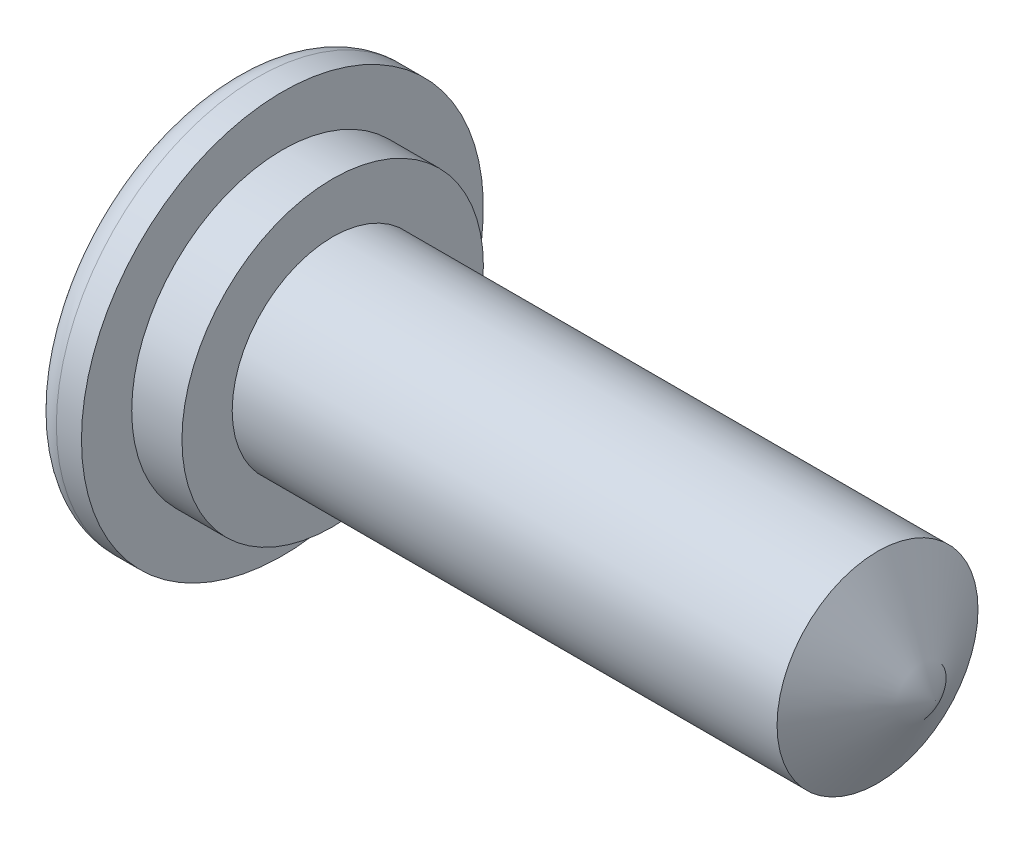
SolidWorks part; units mm, degrees
material "AISI 1020 Acier laminé à froid"
ref_plane "Plan de face" through (0, 0, 0) normal (0, 0, 1) x (1, 0, 0)
ref_plane "Plan de dessus" through (0, 0, 0) normal (0, 1, 0) x (1, 0, 0)
ref_plane "Plan de droite" through (0, 0, 0) normal (1, 0, 0) x (0, 0, -1)
sketch "Esquisse1" plane through (0, 0, 0) normal (0, 0, 1) x (1, 0, 0)
  line L0 (-8.5376, 0) -> (14.4519, 0) construction
  line L1 (0, 3) -> (1, 3)
  line L2 (1, 3) -> (1, 2)
  line L3 (1, 2) -> (11.8453, 2)
  line L4 (11.8453, 2) -> (13, 0)
  line L5 (1.1547, 0) -> (0, 2)
  line L6 (0, 3) -> (0, 4)
  line L7 (0, 2) -> (-0.5, 2)
  line L8 (-1, 2.5) -> (-1, 3.5)
  line L9 (-0.5, 4) -> (0, 4)
  line L10 (1.1547, 0) -> (13, 0)
  arc A0 (-1, 3.5) -> (-0.5, 4) centre (-0.5, 3.5) cw
  arc A1 (-0.5, 2) -> (-1, 2.5) centre (-0.5, 2.5) cw
  dimension "D9" = 0.5
  dimension "D1" = 3
  dimension "D2" = 2
  dimension "D3" = 60
  dimension "D4" = 1
  dimension "D5" = 1
  dimension "D6" = 12
  dimension "D7" = 60
  dimension "D8" = 1
revolve "Révolution1" add sketch "Esquisse1" angle 360 about L0
